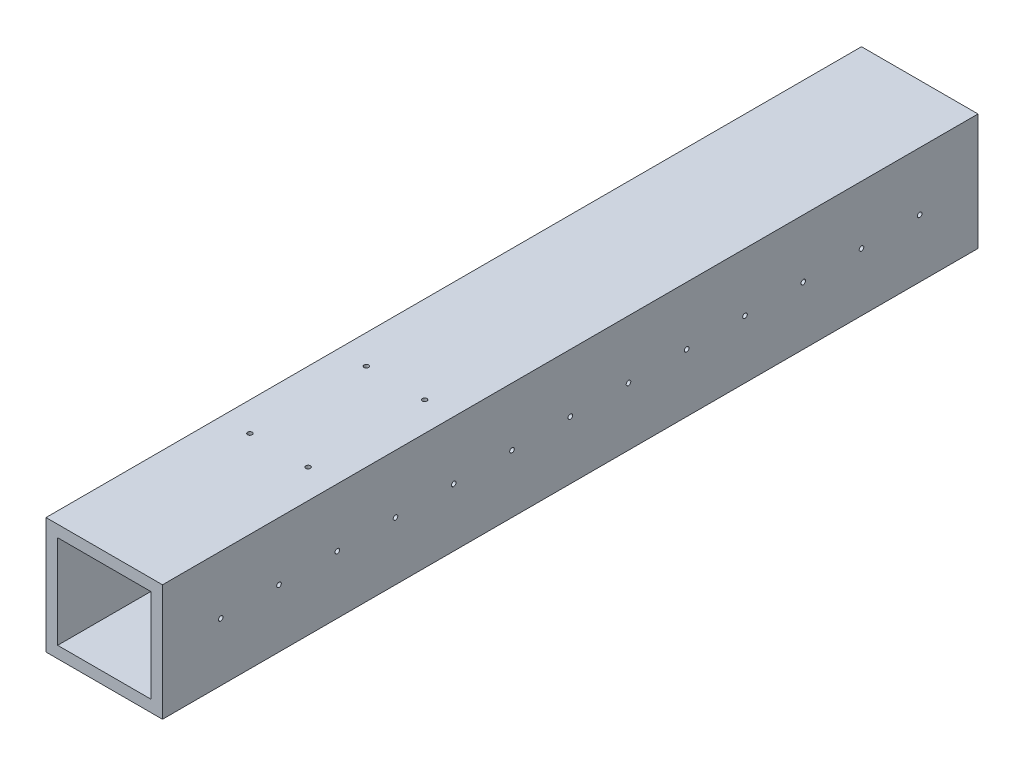
SolidWorks part; units mm, degrees
ref_plane "Front Plane" through (0, 0, 0) normal (0, 0, 1) x (1, 0, 0)
ref_plane "Top Plane" through (0, 0, 0) normal (0, 1, 0) x (1, 0, 0)
ref_plane "Right Plane" through (0, 0, 0) normal (1, 0, 0) x (0, 0, -1)
sketch "Sketch1" plane through (0, 0, 0) normal (0, 0, 1) x (1, 0, 0)
  line L1 (2.0562, 11.0067) -> (22.3762, 11.0067)
  line L2 (2.0562, 11.0067) -> (2.0562, -9.3133)
  line L3 (2.0562, -9.3133) -> (22.3762, -9.3133)
  line L4 (22.3762, 11.0067) -> (22.3762, -9.3133)
  line L5 (-0.4838, 13.5467) -> (24.9162, 13.5467)
  line L6 (-0.4838, 13.5467) -> (-0.4838, -11.8533)
  line L7 (-0.4838, -11.8533) -> (24.9162, -11.8533)
  line L8 (24.9162, 13.5467) -> (24.9162, -11.8533)
  dimension "D1" = 25.4
  dimension "D2" = 25.4
  dimension "D3" = 2.54
  dimension "D4" = 2.54
  dimension "D5" = 2.54
  dimension "D6" = 2.54
extrude "Boss-Extrude1" add sketch "Sketch1" along normal blind 177.8
sketch "Sketch2" plane through (24.9162, 0, 0) normal (1, 0, 0) x (0, 0, -1)
  line L0 (-177.8, 13.5467) -> (0, 13.5467) construction
  line L1 (-177.8, -11.8533) -> (-177.8, 13.5467) construction
  circle A0 centre (-165.1, 0.8467) radius 0.5
  circle A1 centre (-152.4, 0.8467) radius 0.5
  circle A2 centre (-139.7, 0.8467) radius 0.5
  circle A3 centre (-127, 0.8467) radius 0.5
  circle A4 centre (-114.3, 0.8467) radius 0.5
  circle A5 centre (-101.6, 0.8467) radius 0.5
  circle A6 centre (-88.9, 0.8467) radius 0.5
  circle A7 centre (-76.2, 0.8467) radius 0.5
  circle A8 centre (-63.5, 0.8467) radius 0.5
  circle A9 centre (-50.8, 0.8467) radius 0.5
  circle A10 centre (-38.1, 0.8467) radius 0.5
  circle A11 centre (-25.4, 0.8467) radius 0.5
  circle A12 centre (-12.7, 0.8467) radius 0.5
  dimension "D1" = 1
  dimension "D2" = 12.7
  dimension "D3" = 12.7
  dimension "D4" = 13
extrude "Cut-Extrude1" cut sketch "Sketch2" against normal through all both and the other way through all
sketch "Sketch4" plane through (0, -11.8533, 0) normal (0, -1, 0) x (-1, 0, 0)
  circle A0 centre (-5.8662, -139.7) radius 0.5
  circle A1 centre (-5.8662, -139.7) radius 2 construction
  circle A2 centre (-18.5662, -139.7) radius 0.5
  circle A3 centre (-5.8662, -114.3) radius 0.5
  circle A4 centre (-18.5662, -114.3) radius 0.5
  circle A5 centre (-18.5662, -139.7) radius 2 construction
  circle A6 centre (-5.8662, -114.3) radius 2 construction
  circle A7 centre (-18.5662, -114.3) radius 2 construction
  dimension "D1" = 1
  dimension "D2" = 1
  dimension "D3" = 1
  dimension "D4" = 1
extrude "Cut-Extrude3" cut sketch "Sketch4" against normal through all
